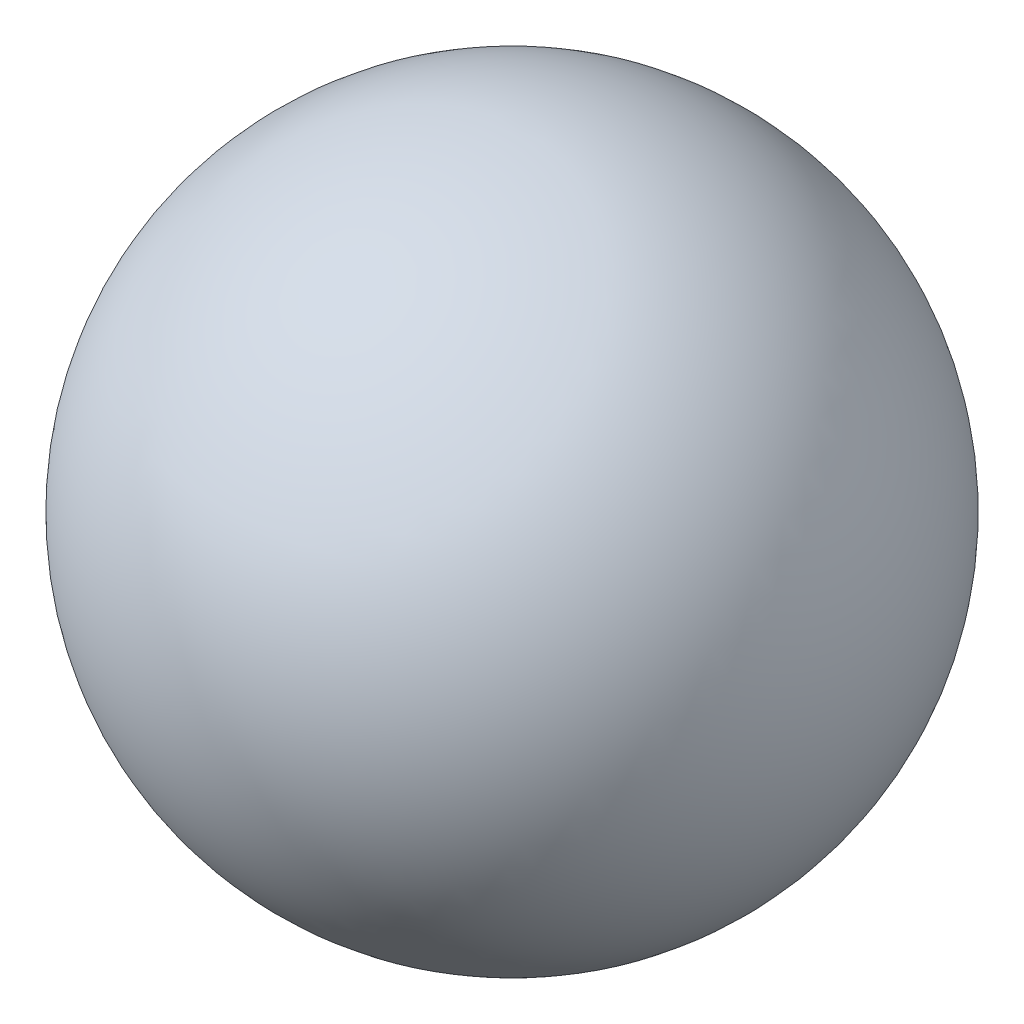
SolidWorks part; units mm, degrees
ref_plane "前视基准面" through (0, 0, 0) normal (0, 0, 1) x (1, 0, 0)
ref_plane "上视基准面" through (0, 0, 0) normal (0, 1, 0) x (1, 0, 0)
ref_plane "右视基准面" through (0, 0, 0) normal (1, 0, 0) x (0, 0, -1)
sketch "草图1" plane through (0, 0, 0) normal (0, 0, 1) x (1, 0, 0)
  line L0 (0, 1.8) -> (0, -1.8)
  arc A0 (0, 1.8) -> (0, -1.8) centre (0, 0) ccw
revolve "旋转1" add sketch "草图1" angle 360 about L0
